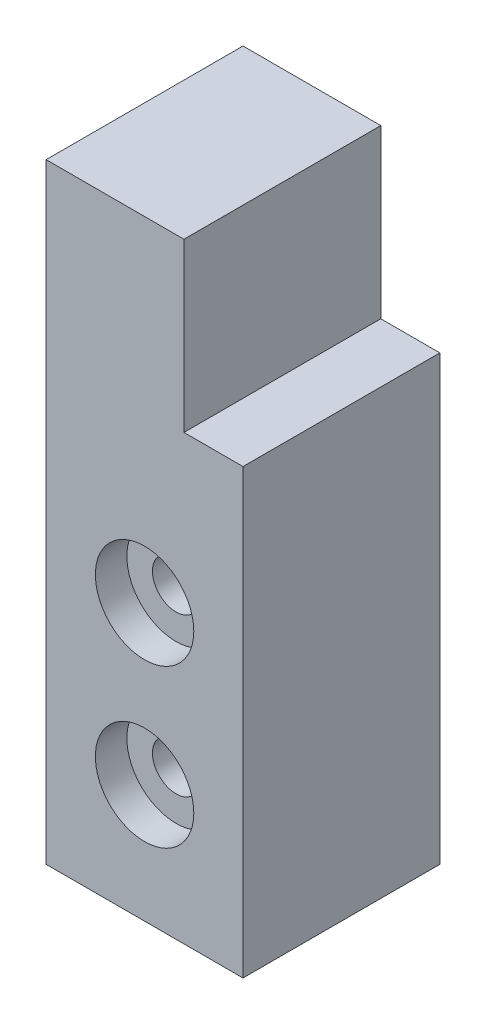
SolidWorks part; units mm, degrees
ref_plane "正面" through (0, 0, 0) normal (0, 0, 1) x (1, 0, 0)
ref_plane "平面" through (0, 0, 0) normal (0, 1, 0) x (1, 0, 0)
ref_plane "右側面" through (0, 0, 0) normal (1, 0, 0) x (0, 0, -1)
sketch "Sketch1" plane through (0, 0, 0) normal (0, 0, 1) x (1, 0, 0)
  line L1 (0, 0) -> (10, 0)
  line L2 (0, 0) -> (0, 31)
  line L3 (0, 31) -> (10, 31)
  line L4 (10, 0) -> (10, 31)
extrude "Boss-Extrude1" add sketch "Sketch1" along normal blind 10
sketch "Sketch2" plane through (0, 0, 10) normal (0, 0, 1) x (1, 0, 0)
  line L1 (10, 31) -> (7, 31)
  line L2 (10, 31) -> (10, 22.5)
  line L3 (10, 22.5) -> (7, 22.5)
  line L4 (7, 31) -> (7, 22.5)
extrude "Cut-Extrude1" cut sketch "Sketch2" against normal blind 10
hole_wizard "CBORE for M2 Pan Head Screw1" positions "Sketch3" profile "Sketch4" counterbore size "M2" standard "JIS"
sketch "Sketch3" plane through (0, 0, 10) normal (0, 0, 1) x (1, 0, 0)
  line L1 (0, 31) -> (0, 0) construction
  line L2 (0, 0) -> (10, 0) construction
  point P0 (5, 14)
  point P2 (5, 6)
  dimension "D1" = 5
  dimension "D2" = 5
  dimension "D3" = 6
  dimension "D4" = 14
sketch "Sketch4" plane through (5, 14, 10) normal (1, 0, 0) x (0, -1, 0)
  line L0 (0, 0) -> (0, 10.721)
  line L1 (0, 10.721) -> (1.2, 10)
  line L2 (1.2, 10) -> (1.2, 1.6)
  line L3 (1.2, 1.6) -> (2.5, 1.6)
  line L4 (2.5, 1.6) -> (2.5, 0)
  line L5 (2.5, 0) -> (0, 0)
  line L10 (0, 10.721) -> (-1.2, 10) construction
  line L11 (0, -6.35) -> (0, 107.95) construction
  dimension "Hole Dia." = 2.4
  dimension "Hole Depth" = 10
  dimension "C'Bore Dia." = 5
  dimension "C'Bore Depth" = 1.6
  dimension "Drill Angle" = 118
